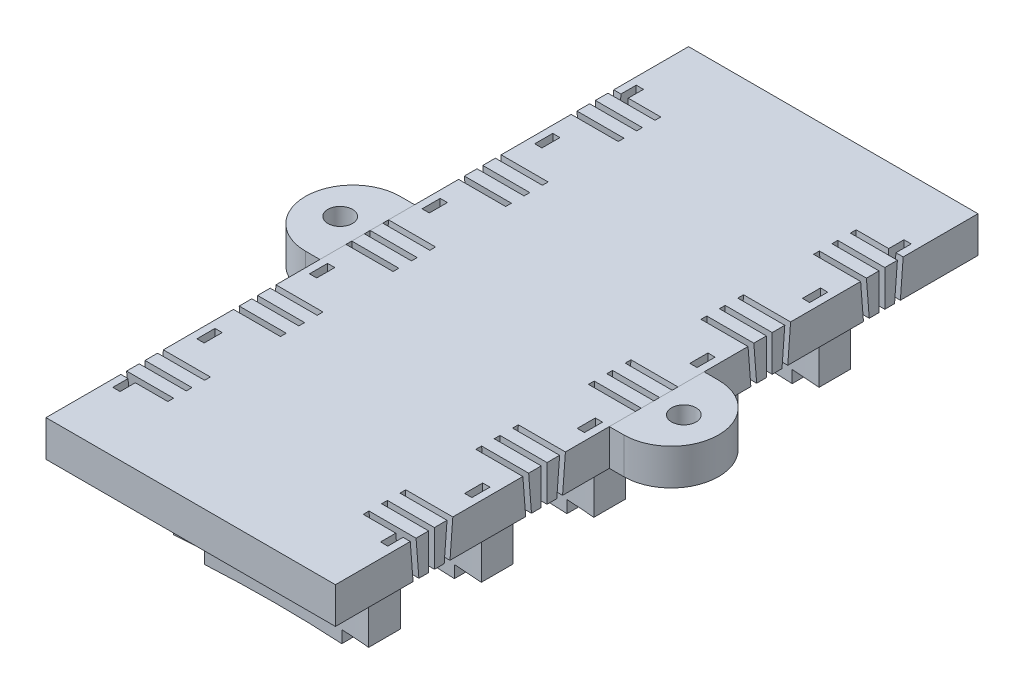
SolidWorks part; units mm, degrees
ref_plane "Спереди" through (0, 0, 0) normal (0, 0, 1) x (1, 0, 0)
ref_plane "Сверху" through (0, 0, 0) normal (0, 1, 0) x (1, 0, 0)
ref_plane "Справа" through (0, 0, 0) normal (1, 0, 0) x (0, 0, -1)
sketch "Эскиз2" plane through (0, 0, 0) normal (0, 1, 0) x (1, 0, 0)
  line L5 (20, -44.4) -> (-20, -44.4)
  line L6 (20, -44.4) -> (20, 44.4)
  line L7 (20, 44.4) -> (-20, 44.4)
  line L8 (-20, -44.4) -> (-20, 44.4)
  line L9 (20, -44.4) -> (-20, 44.4) construction
  line L10 (20, 44.4) -> (-20, -44.4) construction
  point P0 (0, 0)
  dimension "D1" = 88.8
  dimension "D2" = 40
extrude "Бобышка-Вытянуть1" add sketch "Эскиз2" along normal blind 18
sketch "Эскиз7" plane through (0, 0, 0) normal (0, -1, 0) x (1, 0, 0)
  line L72 (20, 44.4) -> (20, -44.4) construction
  line L73 (-20, 44.4) -> (20, 44.4)
  line L74 (-20, 44.4) -> (-20, 33.35)
  line L76 (20, 44.4) -> (20, 33.35)
  line L77 (-20, -44.4) -> (-20, 44.4) construction
  line L79 (-20, 28.89) -> (-20, 17.79)
  line L81 (20, 28.89) -> (20, 17.79)
  line L82 (-20, 33.35) -> (-14, 33.35)
  line L88 (-20, 13.33) -> (-20, 2.23)
  line L90 (20, 13.33) -> (20, 2.23)
  line L92 (-20, -2.23) -> (-20, -13.33)
  line L94 (20, -2.23) -> (20, -13.33)
  line L96 (-20, -33.35) -> (-20, -44.4)
  line L97 (-20, -44.4) -> (20, -44.4)
  line L98 (20, -33.35) -> (20, -44.4)
  line L100 (-20, -17.79) -> (-20, -28.89)
  line L102 (20, -17.79) -> (20, -28.89)
  line L103 (20, 28.89) -> (14, 28.89)
  line L104 (-20, 17.79) -> (-14, 17.79)
  line L105 (20, 13.33) -> (14, 13.33)
  line L106 (-20, 2.23) -> (-14, 2.23)
  line L107 (20, -2.23) -> (14, -2.23)
  line L108 (-20, -13.33) -> (-14, -13.33)
  line L109 (20, -17.79) -> (14, -17.79)
  line L110 (-20, -28.89) -> (-14, -28.89)
  line L111 (20, -33.35) -> (14, -33.35)
  line L112 (14, 33.35) -> (20, 33.35)
  line L113 (-14, 28.89) -> (-20, 28.89)
  line L114 (14, 17.79) -> (20, 17.79)
  line L115 (-14, 13.33) -> (-20, 13.33)
  line L116 (14, 2.23) -> (20, 2.23)
  line L117 (-14, -2.23) -> (-20, -2.23)
  line L118 (14, -13.33) -> (20, -13.33)
  line L119 (-14, -17.79) -> (-20, -17.79)
  line L120 (14, -28.89) -> (20, -28.89)
  line L121 (-14, -33.35) -> (-20, -33.35)
  arc A10 (-14, 33.35) -> (14, 33.35) centre (0, 196.3833) ccw
  arc A11 (-14, 28.89) -> (14, 28.89) centre (0, -134.1433) cw
  arc A12 (-14, 17.79) -> (14, 17.79) centre (0, 180.8233) ccw
  arc A13 (-14, 13.33) -> (14, 13.33) centre (0, -149.7033) cw
  arc A14 (-14, 2.23) -> (14, 2.23) centre (0, 165.2633) ccw
  arc A15 (-14, -2.23) -> (14, -2.23) centre (0, -165.2633) cw
  arc A16 (-14, -13.33) -> (14, -13.33) centre (0, 149.7033) ccw
  arc A17 (-14, -17.79) -> (14, -17.79) centre (0, -180.8233) cw
  arc A18 (-14, -28.89) -> (14, -28.89) centre (0, 134.1433) ccw
  arc A19 (-14, -33.35) -> (14, -33.35) centre (0, -196.3833) cw
  point P36 (0, 32.75)
  point P37 (0, 29.49)
  point P39 (-101.1567, 30.7829)
  dimension "D6" = 6
  dimension "D4" = 6
  dimension "D1" = 11.05
  dimension "D5" = 6
  dimension "D8" = 6
  dimension "D9" = 11.1
  dimension "D10" = 0.6
  dimension "D11" = 0.6
  dimension "D12" = 5
extrude "Вырез-Вытянуть1" cut sketch "Эскиз7" against normal blind 13
sketch "Эскиз3" plane through (0, 13, 0) normal (0, 1, 0) x (1, 0, 0)
  line L4 (0, -9.9) -> (0, 9.9) construction
  line L13 (-22, 6.55) -> (-20, 6.55)
  line L19 (-22, -6.55) -> (-20, -6.55)
  line L20 (22, 6.55) -> (20, 6.55)
  line L21 (22, -6.55) -> (20, -6.55)
  line L22 (20, -44.4) -> (20, 44.4) construction
  line L24 (20, 6.55) -> (20, -6.55)
  line L25 (-20, -6.55) -> (-20, 6.55)
  line L26 (-20, 44.4) -> (-20, -44.4) construction
  line L27 (-20, -44.4) -> (20, -44.4) construction
  arc A2 (-22, 6.55) -> (-22, -6.55) centre (-22, 0) ccw
  arc A3 (22, 6.55) -> (22, -6.55) centre (22, 0) cw
  dimension "D1" = 13.1
  dimension "D2" = 22
  dimension "D3" = 44.4
  dimension "D4" = 44.4
extrude "Бобышка-Вытянуть2" add sketch "Эскиз3" along normal up to surface (5 mm away) separate body up to face at (0, 18, 0)
hole_wizard "Отверстие с зазором M31" positions "Эскиз10" profile "Эскиз11" hole size "M3" standard "JIS" end condition up to next
sketch "Эскиз10" plane through (0, 13, 0) normal (0, -1, 0) x (-1, 0, 0)
  point P0 (-23.75, 0)
  point P2 (23.75, 0)
  dimension "D1" = 23.75
  dimension "D2" = 23.75
sketch "Эскиз11" plane through (23.75, 13, 0) normal (1, 0, 0) x (0, 0, -1)
  line L0 (0, 0) -> (0, 5.001)
  line L1 (0, 5.001) -> (1.7, 5.001)
  line L2 (1.7, 5.001) -> (1.7, 0)
  line L5 (1.7, 0) -> (0, 0)
  line L11 (0, -6.35) -> (0, 107.95) construction
  dimension "Диаметр сквозного отверстия" = 3.4
  dimension "Глубина сквозного отверстия" = 5.001
sketch "Эскиз18" plane through (20, 0, 0) normal (1, 0, 0) x (0, 0, -1)
  line L35 (-17.79, 13) -> (-13.33, 13)
  line L36 (-17.79, 13) -> (-17.79, 0)
  line L37 (-17.79, 0) -> (-13.33, 0)
  line L38 (-13.33, 13) -> (-13.33, 0)
extrude "Вырез-Вытянуть5" cut sketch "Эскиз18" against normal blind 6.5
sketch "Эскиз19" plane through (20, 0, 0) normal (1, 0, 0) x (0, 0, -1)
  line L0 (-44.4, 18) -> (44.4, 18) construction
  line L1 (-31.52, 18) -> (-30.72, 18)
  line L2 (-31.52, 18) -> (-31.52, 1)
  line L3 (-31.52, 1) -> (-30.72, 1)
  line L4 (-30.72, 18) -> (-30.72, 1)
  line L6 (-2.23, 13) -> (-28.89, 13) construction
  line L8 (-34.06, 18) -> (-33.26, 18)
  line L10 (-33.67, 13) -> (-32.87, 13)
  line L13 (-28.98, 18) -> (-28.18, 18)
  line L15 (-29.37, 13) -> (-28.57, 13)
  line L17 (-34.06, 18) -> (-33.67, 13)
  line L18 (-33.26, 18) -> (-32.87, 13)
  line L19 (-28.98, 18) -> (-29.37, 13)
  line L20 (-28.18, 18) -> (-28.57, 13)
  line L21 (-33.35, 13) -> (-33.35, 0) construction
  line L23 (-33.35, 0) -> (-28.89, 0) construction
  point P22 (0, 0)
  dimension "D1" = 0.8
  dimension "D2" = 1.83
  dimension "D3" = 0.8
  dimension "D4" = 0.8
  dimension "D5" = 2.54
  dimension "D6" = 2.54
  dimension "D7" = 0.8
  dimension "D8" = 1.35
  dimension "D9" = 0.8
  dimension "D10" = 1.35
  dimension "D11" = 0
  dimension "D12" = 0
  dimension "D13" = 1
extrude "Вырез-Вытянуть6" cut sketch "Эскиз19" against normal blind 6.5
mirror "Зеркальное отражение5" about plane through (0, 0, 0) normal (1, 0, 0) of "Вырез-Вытянуть6"
mirror "Зеркальное отражение6" about plane through (0, 0, 0) normal (1, 0, 0) of "Вырез-Вытянуть5"
pattern_linear "Линейный массив9" count 2 spacing 15.56 along (0, 0, -1) count 4 spacing 15.56 along (0, 0, -1) of "Зеркальное отражение6", "Вырез-Вытянуть5"
pattern_linear "Линейный массив10" count 5 spacing 15.56 along (0, 0, -1) of "Зеркальное отражение5", "Вырез-Вытянуть6"
sketch "Эскиз21" plane through (0, 13, 0) normal (0, -1, 0) x (1, 0, 0)
  line L1 (19, -33.67) -> (18, -33.67)
  line L2 (19, -33.67) -> (19, -36.17)
  line L3 (19, -36.17) -> (18, -36.17)
  line L4 (18, -33.67) -> (18, -36.17)
  line L5 (20, -44.4) -> (20, -33.67) construction
  line L7 (-19, -36.17) -> (-18, -36.17)
  line L8 (-19, -36.17) -> (-19, -33.67)
  line L9 (-19, -33.67) -> (-18, -33.67)
  line L10 (-18, -36.17) -> (-18, -33.67)
  line L11 (-20, -33.67) -> (-20, -44.4) construction
  line L12 (13.5, -33.67) -> (20, -33.67) construction
  line L13 (-13.5, -33.67) -> (-20, -33.67) construction
  dimension "D1" = 1
  dimension "D2" = 1
  dimension "D3" = 2.5
  dimension "D4" = 1
  dimension "D5" = 1
  dimension "D6" = 2.5
  dimension "D7" = 0
  dimension "D8" = 0
extrude "Вырез-Вытянуть8" cut sketch "Эскиз21" against normal up to next (5 mm away)
mirror "Зеркальное отражение7" about plane through (0, 0, 0) normal (0, 0, 1) of "Вырез-Вытянуть8"
sketch "Эскиз22" plane through (0, 13, 0) normal (0, -1, 0) x (1, 0, 0)
  line L1 (-19, -22.1322) -> (-18, -22.1322)
  line L2 (-19, -22.1322) -> (-19, -24.6322)
  line L3 (-19, -24.6322) -> (-18, -24.6322)
  line L4 (-18, -22.1322) -> (-18, -24.6322)
  line L5 (18, -22.1322) -> (19, -22.1322)
  line L6 (18, -22.1322) -> (18, -24.6322)
  line L7 (18, -24.6322) -> (19, -24.6322)
  line L8 (19, -22.1322) -> (19, -24.6322)
  line L10 (20, -28.57) -> (20, -18.11) construction
  line L14 (-20, -18.11) -> (-20, -28.57) construction
  point P17 (-20, -23.34)
  dimension "D1" = 2.5
  dimension "D2" = 2.5
  dimension "D3" = 1
  dimension "D4" = 1
  dimension "D6" = 1
  dimension "D7" = 4.3
  dimension "D8" = 1
  dimension "D9" = 4.3
extrude "Вырез-Вытянуть9" cut sketch "Эскиз22" against normal up to next (5 mm away)
pattern_linear "Линейный массив12" count 4 spacing 15.56 along (0, 0, 1) of "Вырез-Вытянуть9"
sketch "Эскиз24" plane through (0, 0, 0) normal (0, -1, 0) x (1, 0, 0)
  line L0 (-13.5, 33.35) -> (-13.5, 28.89)
  line L1 (-13.5, 33.35) -> (-9.5, 33.35)
  line L2 (-13.5, 28.89) -> (-9.5, 28.89)
  line L3 (-9.5, 33.35) -> (-9.5, 28.89)
  line L4 (9.5, 33.35) -> (9.5, 28.89)
  line L5 (9.5, 33.35) -> (13.5, 33.35)
  line L6 (9.5, 28.89) -> (13.5, 28.89)
  line L7 (13.5, 33.35) -> (13.5, 28.89)
  line L8 (9.5, 17.79) -> (9.5, 13.33)
  line L9 (9.5, 17.79) -> (13.5, 17.79)
  line L10 (9.5, 13.33) -> (13.5, 13.33)
  line L11 (13.5, 17.79) -> (13.5, 13.33)
  line L12 (9.5, 2.23) -> (9.5, -2.23)
  line L13 (9.5, 2.23) -> (13.5, 2.23)
  line L14 (9.5, -2.23) -> (13.5, -2.23)
  line L15 (13.5, 2.23) -> (13.5, -2.23)
  line L16 (9.5, -13.33) -> (9.5, -17.79)
  line L17 (9.5, -13.33) -> (13.5, -13.33)
  line L18 (9.5, -17.79) -> (13.5, -17.79)
  line L19 (13.5, -13.33) -> (13.5, -17.79)
  line L20 (9.5, -28.89) -> (9.5, -33.35)
  line L21 (9.5, -28.89) -> (13.5, -28.89)
  line L22 (9.5, -33.35) -> (13.5, -33.35)
  line L23 (13.5, -28.89) -> (13.5, -33.35)
  line L24 (-13.5, 17.79) -> (-13.5, 13.33)
  line L25 (-13.5, 17.79) -> (-9.5, 17.79)
  line L26 (-13.5, 13.33) -> (-9.5, 13.33)
  line L27 (-9.5, 17.79) -> (-9.5, 13.33)
  line L28 (-13.5, 2.23) -> (-13.5, -2.23)
  line L29 (-13.5, 2.23) -> (-9.5, 2.23)
  line L30 (-13.5, -2.23) -> (-9.5, -2.23)
  line L31 (-9.5, 2.23) -> (-9.5, -2.23)
  line L32 (-13.5, -13.33) -> (-13.5, -17.79)
  line L33 (-13.5, -13.33) -> (-9.5, -13.33)
  line L34 (-13.5, -17.79) -> (-9.5, -17.79)
  line L35 (-9.5, -13.33) -> (-9.5, -17.79)
  line L36 (-13.5, -28.89) -> (-13.5, -33.35)
  line L37 (-13.5, -28.89) -> (-9.5, -28.89)
  line L38 (-13.5, -33.35) -> (-9.5, -33.35)
  line L39 (-9.5, -28.89) -> (-9.5, -33.35)
  point P0 (0, 0)
  dimension "D1" = 0.0422
  dimension "D4" = 19
  dimension "D5" = 4.46
  dimension "D2" = 2
  dimension "D3" = 5
extrude "Вырез-Вытянуть10" cut sketch "Эскиз24" against normal blind 1.7
